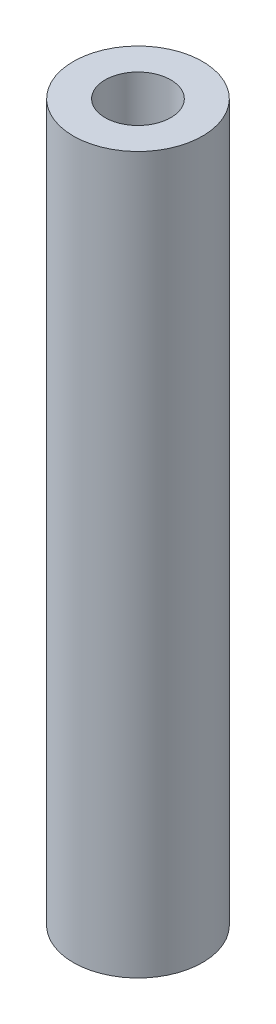
SolidWorks part; units mm, degrees
ref_plane "Plano frontal" through (0, 0, 0) normal (0, 0, 1) x (1, 0, 0)
ref_plane "Plano superior" through (0, 0, 0) normal (0, 1, 0) x (1, 0, 0)
ref_plane "Plano direito" through (0, 0, 0) normal (1, 0, 0) x (0, 0, -1)
sketch "Esboço2" plane through (0, 0, 0) normal (0, 1, 0) x (1, 0, 0)
  circle A0 centre (0, 0) radius 3.25
extrude "Ressalto-extrusão1" add sketch "Esboço2" along normal mid plane 36
hole_wizard "Furo roscado de M41" positions "3DSketch2" profile "Esboço4" tap size "M4" standard "ISO" end condition through all
sketch3d "3DSketch2"
  point P0 (0, 0, 0)
  point P3 (0, 0, 0)
  point P5 (0, 0, 0)
  point P7 (0, 0, 0)
  point P9 (0, 0, 0)
  point P11 (0, 18, 0)
sketch "Esboço4" plane through (0, 18, 0) normal (1, 0, 0) x (0, 0, 1)
  line L0 (0, 0) -> (0, 36)
  line L1 (0, 36) -> (2.025, 36)
  line L2 (1.65, 35.625) -> (1.65, 0)
  line L5 (1.65, 0) -> (0, 0)
  line L7 (2.025, 36) -> (1.65, 35.625)
  line L8 (-2.025, 36) -> (-1.65, 35.625) construction
  line L11 (0, -6.35) -> (0, 107.95) construction
  dimension "Thru Tap Drill Dia." = 3.3
  dimension "Thru Tap Drill Depth" = 36
  dimension "Far C'Sink Dia." = 4.05
  dimension "Far C'Sink Angle" = 90
cosmetic thread "Rosca de furo1" parameters "D2"=4
cosmetic thread "Rosca de furo2" parameters "D2"=4
cosmetic thread "Rosca de furo3" parameters "D2"=4
cosmetic thread "Rosca de furo4" parameters "D2"=4
cosmetic thread "Rosca de furo5" parameters "D2"=4
cosmetic thread "Rosca de furo6" parameters "D2"=4
